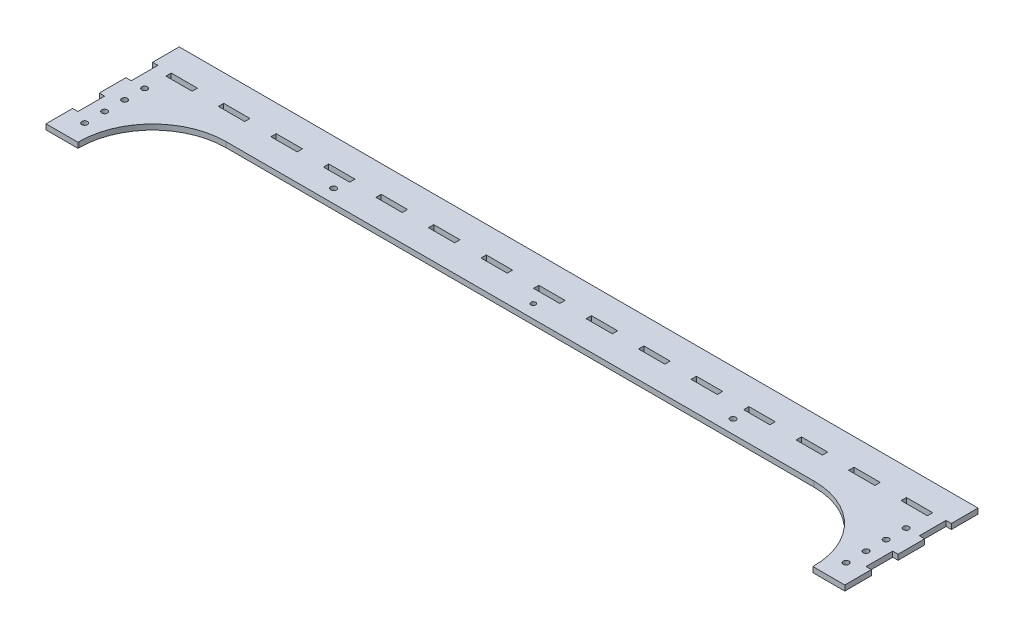
SolidWorks part; units mm, degrees
ref_plane "Front Plane" through (0, 0, 0) normal (0, 0, 1) x (1, 0, 0)
ref_plane "Top Plane" through (0, 0, 0) normal (0, 1, 0) x (1, 0, 0)
ref_plane "Right Plane" through (0, 0, 0) normal (1, 0, 0) x (0, 0, -1)
sketch "Sketch1" plane through (0, 0, 0) normal (0, 1, 0) x (1, 0, 0)
  line L0 (0, -26.4292) -> (0, 52.5615) construction
  line L1 (299.8, 24) -> (299.8, 4)
  line L2 (285.8, -44.149) -> (285.8, -73.2727) construction
  line L3 (299.8, -76) -> (275.8, -76)
  line L4 (275.8, -76) -> (275.8, -75)
  line L5 (220.8, -20) -> (-220.8, -20)
  line L6 (-9.8625, 0) -> (9.8625, 0)
  line L7 (9.8625, 0) -> (9.8625, 4)
  line L8 (9.8625, 4) -> (-9.8625, 4)
  line L9 (29.5875, 4) -> (29.5875, 0)
  line L10 (29.5875, 0) -> (49.3125, 0)
  line L11 (49.3125, 0) -> (49.3125, 4)
  line L12 (49.3125, 4) -> (29.5875, 4)
  line L13 (88.7325, 4) -> (69.0075, 4)
  line L14 (69.0075, 4) -> (69.0075, 0)
  line L15 (69.0075, 0) -> (88.7325, 0)
  line L16 (88.7325, 0) -> (88.7325, 4)
  line L17 (128.1525, 4) -> (108.4275, 4)
  line L18 (108.4275, 4) -> (108.4275, 0)
  line L19 (108.4275, 0) -> (128.1525, 0)
  line L20 (128.1525, 0) -> (128.1525, 4)
  line L21 (167.5725, 4) -> (147.8475, 4)
  line L22 (147.8475, 4) -> (147.8475, 0)
  line L23 (147.8475, 0) -> (167.5725, 0)
  line L24 (167.5725, 0) -> (167.5725, 4)
  line L25 (206.9925, 4) -> (187.2675, 4)
  line L26 (187.2675, 4) -> (187.2675, 0)
  line L27 (187.2675, 0) -> (206.9925, 0)
  line L28 (206.9925, 0) -> (206.9925, 4)
  line L29 (246.4125, 4) -> (226.6875, 4)
  line L30 (226.6875, 4) -> (226.6875, 0)
  line L31 (226.6875, 0) -> (246.4125, 0)
  line L32 (246.4125, 0) -> (246.4125, 4)
  line L33 (285.8325, 4) -> (266.1075, 4)
  line L34 (266.1075, 4) -> (266.1075, 0)
  line L35 (266.1075, 0) -> (285.8325, 0)
  line L36 (285.8325, 0) -> (285.8325, 4)
  line L37 (299.8, 4) -> (295.8, 4)
  line L38 (295.8, 4) -> (295.8, -16)
  line L39 (299.8, 24) -> (-299.8, 24)
  line L40 (295.8, -16) -> (299.8, -16)
  line L41 (299.8, -16) -> (299.8, -36)
  line L42 (299.8, -36) -> (295.8, -36)
  line L43 (295.8, -36) -> (295.8, -56)
  line L44 (295.8, -56) -> (299.8, -56)
  line L45 (299.8, -56) -> (299.8, -76)
  line L46 (-285.8, -44.149) -> (-285.8, -73.2727) construction
  line L47 (-299.8, -56) -> (-299.8, -76)
  line L48 (-295.8, -56) -> (-299.8, -56)
  line L49 (-295.8, -36) -> (-295.8, -56)
  line L50 (-299.8, -36) -> (-295.8, -36)
  line L51 (-299.8, -16) -> (-299.8, -36)
  line L52 (-295.8, -16) -> (-299.8, -16)
  line L53 (-295.8, 4) -> (-295.8, -16)
  line L54 (-299.8, 4) -> (-295.8, 4)
  line L55 (-285.8325, 0) -> (-285.8325, 4)
  line L56 (-266.1075, 0) -> (-285.8325, 0)
  line L57 (-266.1075, 4) -> (-266.1075, 0)
  line L58 (-285.8325, 4) -> (-266.1075, 4)
  line L59 (-246.4125, 0) -> (-246.4125, 4)
  line L60 (-226.6875, 0) -> (-246.4125, 0)
  line L61 (-226.6875, 4) -> (-226.6875, 0)
  line L62 (-246.4125, 4) -> (-226.6875, 4)
  line L63 (-206.9925, 0) -> (-206.9925, 4)
  line L64 (-187.2675, 0) -> (-206.9925, 0)
  line L65 (-187.2675, 4) -> (-187.2675, 0)
  line L66 (-206.9925, 4) -> (-187.2675, 4)
  line L67 (-167.5725, 0) -> (-167.5725, 4)
  line L68 (-147.8475, 0) -> (-167.5725, 0)
  line L69 (-147.8475, 4) -> (-147.8475, 0)
  line L70 (-167.5725, 4) -> (-147.8475, 4)
  line L71 (-128.1525, 0) -> (-128.1525, 4)
  line L72 (-108.4275, 0) -> (-128.1525, 0)
  line L73 (-108.4275, 4) -> (-108.4275, 0)
  line L74 (-128.1525, 4) -> (-108.4275, 4)
  line L75 (-88.7325, 0) -> (-88.7325, 4)
  line L76 (-69.0075, 0) -> (-88.7325, 0)
  line L77 (-69.0075, 4) -> (-69.0075, 0)
  line L78 (-88.7325, 4) -> (-69.0075, 4)
  line L79 (-49.3125, 4) -> (-29.5875, 4)
  line L80 (-49.3125, 0) -> (-49.3125, 4)
  line L81 (-29.5875, 0) -> (-49.3125, 0)
  line L82 (-29.5875, 4) -> (-29.5875, 0)
  line L83 (-9.8625, 0) -> (-9.8625, 4)
  line L84 (-275.8, -76) -> (-275.8, -75)
  line L85 (-299.8, -76) -> (-275.8, -76)
  line L86 (-299.8, 24) -> (-299.8, 4)
  line L87 (258.2275, -38.5) -> (311.1408, -38.5) construction
  line L88 (-254.1866, -10) -> (30.8656, -10) construction
  circle A0 centre (285.8, -61) radius 2.125
  circle A1 centre (285.8, -46) radius 2.125
  circle A2 centre (-285.8, -46) radius 2.125
  circle A3 centre (-285.8, -61) radius 2.125
  arc A4 (275.8, -75) -> (220.8, -20) centre (220.8, -75) ccw
  arc A5 (-275.8, -75) -> (-220.8, -20) centre (-220.8, -75) cw
  circle A6 centre (285.8, -16) radius 2.125
  circle A7 centre (285.8, -31) radius 2.125
  circle A8 centre (-285.8, -31) radius 2.125
  circle A9 centre (-285.8, -16) radius 2.125
  circle A10 centre (-149.9, -10) radius 2.125
  circle A14 centre (149.9, -10) radius 2.125
  circle A15 centre (0, -10) radius 1.7871
  point P69 (0, 24)
  point P100 (0, 4)
  point P101 (0, 0)
  point P102 (0, -20)
  point P105 (275.8, -20)
  point P108 (-275.8, -20)
  dimension "D11" = 4.25
  dimension "D17" = 55
  dimension "D1" = 24
  dimension "D2" = 10
  dimension "D3" = 299.8
  dimension "D4" = 24
  dimension "D5" = 20
  dimension "D6" = 9.8625
  dimension "D7" = 4
  dimension "D8" = 19.725
  dimension "D9" = 19.725
  dimension "D12" = 15
  dimension "D13" = 15
  dimension "D14" = 100
  dimension "D15" = 20
  dimension "D16" = 4
  dimension "D18" = 7.5
  dimension "D19" = 10
  dimension "D20" = 149.9
  dimension "D10" = 7
extrude "Boss-Extrude1" add sketch "Sketch1" along normal blind 4
